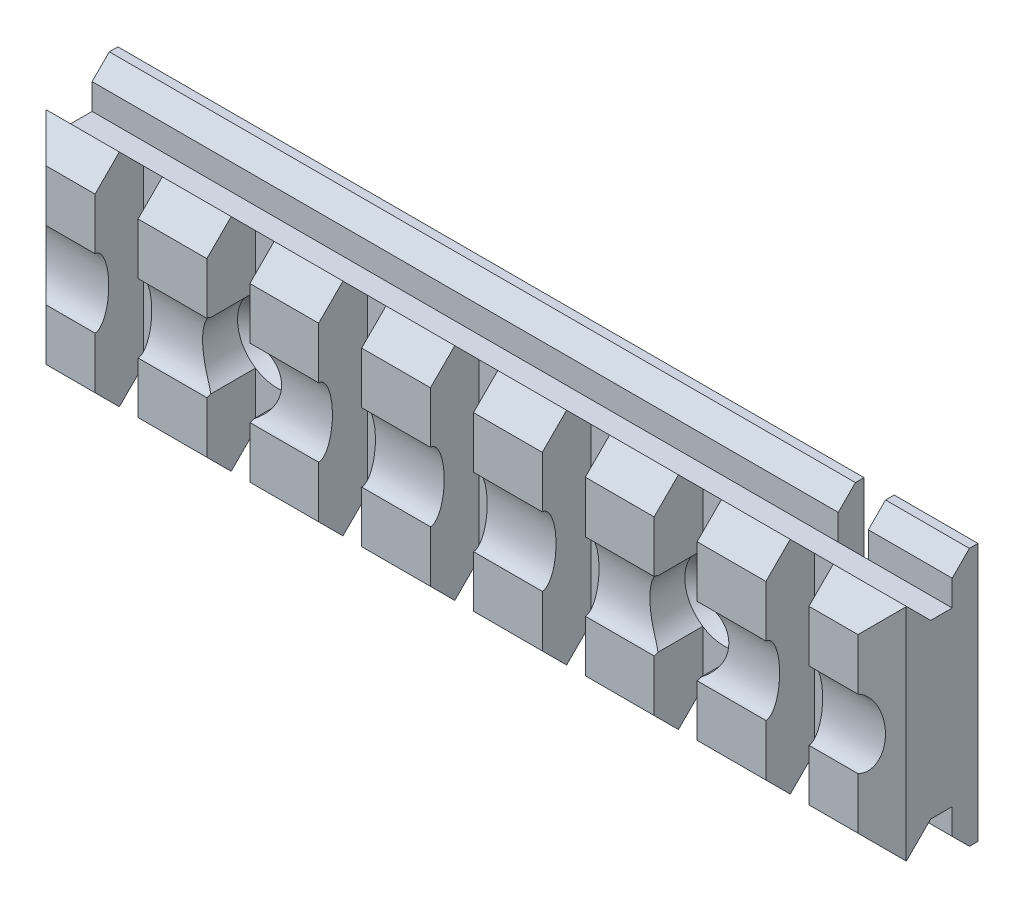
SolidWorks part; units mm, degrees
ref_plane "Ebene vorne" through (0, 0, 0) normal (0, 0, 1) x (1, 0, 0)
ref_plane "Ebene oben" through (0, 0, 0) normal (0, 1, 0) x (1, 0, 0)
ref_plane "Ebene rechts" through (0, 0, 0) normal (1, 0, 0) x (0, 0, -1)
sketch "Skizze1" plane through (0, 0, 0) normal (0, 0, 1) x (1, 0, 0)
  line L1 (-38.5927, 21.3922) -> (61.4073, 21.3922)
  line L2 (-38.5927, 21.3922) -> (-38.5927, -8.6078)
  line L3 (-38.5927, -8.6078) -> (61.4073, -8.6078)
  line L4 (61.4073, 21.3922) -> (61.4073, -8.6078)
  dimension "D1" = 100
  dimension "D2" = 30
extrude "Aufsatz-Linear austragen1" add sketch "Skizze1" along normal blind 3
sketch "Skizze4" plane through (0, 0, 3) normal (0, 0, 1) x (1, 0, 0)
  line L0 (-38.5927, 21.3922) -> (-38.5927, -8.6078) construction
  line L1 (-38.5927, 16.3922) -> (61.4073, 16.3922)
  line L2 (-38.5927, 16.3922) -> (-38.5927, -3.6078)
  line L3 (-38.5927, -3.6078) -> (61.4073, -3.6078)
  line L4 (61.4073, 16.3922) -> (61.4073, -3.6078)
  line L5 (61.4073, -8.6078) -> (61.4073, 21.3922) construction
  line L6 (61.4073, 21.3922) -> (-38.5927, 21.3922) construction
  line L7 (-38.5927, -8.6078) -> (61.4073, -8.6078) construction
  dimension "D1" = 5
  dimension "D2" = 5
extrude "Aufsatz-Linear austragen2" add sketch "Skizze4" along normal blind 2.5
sketch "Skizze7" plane through (61.4073, 0, 0) normal (1, 0, 0) x (0, 0, -1)
  line L0 (-5.5, 16.3922) -> (-8.3284, 19.2206)
  line L1 (-8.3284, 19.2206) -> (-11.1569, 16.3922)
  line L2 (-11.1569, 16.3922) -> (-11.1569, -3.6078)
  line L3 (-11.1569, -3.6078) -> (-8.3284, -6.4363)
  line L4 (-8.3284, -6.4363) -> (-5.5, -3.6078)
  line L6 (-5.5, -3.6078) -> (-5.5, 16.3922) construction
  line L16 (0, -8.6078) -> (0, 21.3922)
  line L17 (0, 21.3922) -> (-3, 21.3922)
  line L18 (-3, 21.3922) -> (-3, 16.3922)
  line L19 (-3, 16.3922) -> (-5.5, 16.3922)
  line L20 (-5.5, 16.3922) -> (-5.5, -3.6078)
  line L21 (-5.5, -3.6078) -> (-3, -3.6078)
  line L22 (-3, -3.6078) -> (-3, -8.6078)
  line L23 (-3, -8.6078) -> (0, -8.6078)
  line L28 (-5.5, 16.3922) -> (-5.5, -3.6078)
  dimension "D1" = 135
  dimension "D2" = 4
  dimension "D3" = 0
extrude "Aufsatz-Linear austragen3" add sketch "Skizze7" against normal up to surface (100 mm away) up to face at (-38.5927, 7.0172, 3.1875)
chamfer "Fase1" distance 2.8 1 edges at (61.4073, 6.3922, 11.1569)
chamfer "Fase2" distance 2.8 1 edges at (-38.5927, 6.3922, 11.1569)
sketch "Skizze8" plane through (0, 0, 11.1569) normal (0, 0, 1) x (1, 0, 0)
  line L0 (-38.5927, 19.2206) -> (61.4073, 19.2206) construction
  line L1 (-30.0927, 19.2206) -> (-25.0927, 19.2206)
  line L2 (-30.0927, 19.2206) -> (-30.0927, -6.4363)
  line L3 (-30.0927, -6.4363) -> (-25.0927, -6.4363)
  line L4 (-25.0927, 19.2206) -> (-25.0927, -6.4363)
  line L5 (-38.5927, -6.4363) -> (61.4073, -6.4363) construction
  line L8 (-38.5927, -6.4078) -> (-38.5927, 19.1922) construction
  dimension "D1" = 5
  dimension "D2" = 8.5
extrude "Schnitt-Linear austragen1" cut sketch "Skizze8" against normal up to vertex (5.6569 mm away) up to point (-38.5927, -3.6079, 5.5)
pattern_linear "Lineares Muster1" count 7 spacing 13 along (1, 0, 0) of "Schnitt-Linear austragen1"
chamfer "Fase3" distance 2 angle 45 1 edges at (11.4073, 21.3922, 3)
chamfer "Fase4" distance 2 angle 45 1 edges at (11.4073, -8.6078, 3)
hole_wizard "Formsenkung für M4 Senkschraube mit Innensechskant1" positions "Skizze10" profile "Skizze9" countersink size "M4" standard "DIN"
sketch "Skizze10" plane through (0, 0, 5.5) normal (0, 0, 1) x (1, 0, 0)
  line L0 (-17.0927, 16.3922) -> (-17.0927, -3.6078) construction
  line L1 (-12.0927, 16.3922) -> (-17.0927, 16.3922) construction
  line L2 (39.9073, 16.3922) -> (34.9073, 16.3922) construction
  line L3 (39.9073, -3.6078) -> (39.9073, 16.3922) construction
  point P0 (-14.5927, 6.3922)
  point P2 (37.4073, 6.3922)
  dimension "D1" = 2.5
  dimension "D2" = 10
  dimension "D3" = 10
  dimension "D4" = 2.5
sketch "Skizze9" plane through (-14.5927, 6.3922, 5.5) normal (1, 0, 0) x (0, -1, 0)
  line L0 (0, 0) -> (0, 5.5)
  line L1 (0, 5.5) -> (2.25, 5.5)
  line L2 (2.25, 5.5) -> (2.25, 2.34)
  line L3 (2.25, 2.34) -> (4.59, 0)
  line L5 (4.59, 0) -> (0, 0)
  line L6 (-2.25, 2.34) -> (-4.59, 0) construction
  line L11 (0, -6.35) -> (0, 107.95) construction
  dimension "Bohrerdurchmesser" = 4.5
  dimension "Bohrungstiefe" = 5.5
  dimension "Senkdurchmesser (Oben)" = 9.18
  dimension "Senkwinkel (Oben)" = 90
ref_plane "Ebene1" through (61.4073, 0, 0) normal (1, 0, 0) x (0, 0, -1)
sketch "Skizze13" plane through (61.4073, 0, 0) normal (1, 0, 0) x (0, 0, -1)
  line L0 (-11.1569, -3.6078) -> (-11.1569, 16.3922) construction
  ellipse E0 centre (-11.1569, 6.3922) end of major axis (-11.1569, 10.3922) minor radius 1.6
extrude "Schnitt-Linear austragen2" cut sketch "Skizze13" against normal through all
sketch "Skizze14" plane through (0, 0, 5.5) normal (0, 0, 1) x (1, 0, 0)
  circle A0 centre (37.4073, 6.3922) radius 4.59
  circle A1 centre (-14.5927, 6.3922) radius 4.59
extrude "Schnitt-Linear austragen3" cut sketch "Skizze14" along normal up to surface (5.6569 mm away) up to face at (-8.0927, 13.3922, 11.1569)
sketch "Skizze15" plane through (0, 0, 0) normal (0, 0, -1) x (-1, 0, 0)
  line L0 (-61.4073, 21.3922) -> (38.5927, 21.3922) construction
  line L1 (-48.1573, 9.8922) -> (-51.6573, 9.8922)
  line L2 (-48.1573, 9.8922) -> (-48.1573, 21.3922)
  line L3 (-48.1573, 21.3922) -> (-51.6573, 21.3922)
  line L4 (-51.6573, 9.8922) -> (-51.6573, 21.3922)
  circle A0 centre (-37.4073, 6.3922) radius 2.25 construction
  dimension "D1" = 3.5
  dimension "D2" = 10.75
  dimension "D3" = 0
  dimension "D4" = 3.5
extrude "Schnitt-Linear austragen4" cut sketch "Skizze15" against normal blind 3
